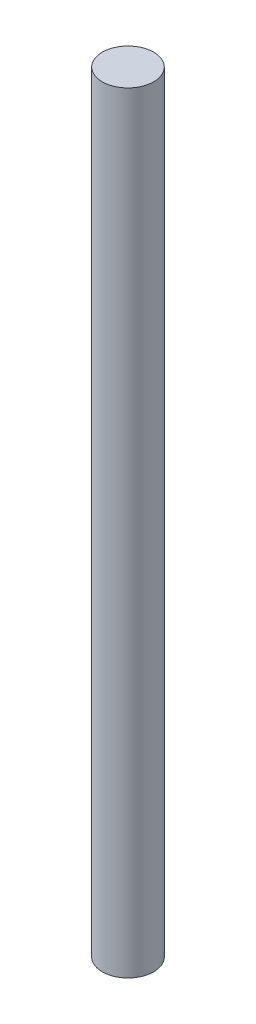
SolidWorks part; units mm, degrees
ref_plane "Alzado" through (0, 0, 0) normal (0, 0, 1) x (1, 0, 0)
ref_plane "Planta" through (0, 0, 0) normal (0, 1, 0) x (1, 0, 0)
ref_plane "Vista lateral" through (0, 0, 0) normal (1, 0, 0) x (0, 0, -1)
sketch "Croquis1" plane through (0, 0, 0) normal (0, 1, 0) x (1, 0, 0)
  circle A0 centre (0, 0) radius 2.5
  dimension "D1" = 5
extrude "Saliente-Extruir1" add sketch "Croquis1" along normal blind 75
